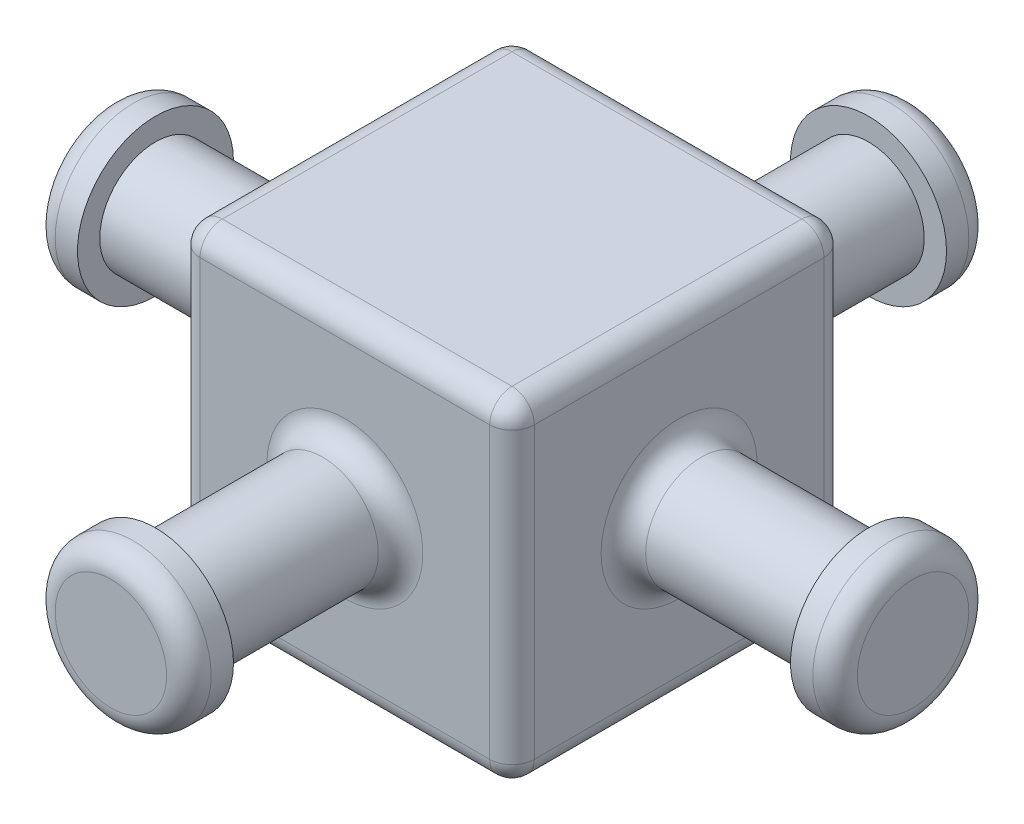
SolidWorks part; units mm, degrees
ref_plane "Front Plane" through (0, 0, 0) normal (0, 0, 1) x (1, 0, 0)
ref_plane "Top Plane" through (0, 0, 0) normal (0, 1, 0) x (1, 0, 0)
ref_plane "Right Plane" through (0, 0, 0) normal (1, 0, 0) x (0, 0, -1)
sketch "Sketch1" plane through (0, 0, 0) normal (0, 0, 1) x (1, 0, 0)
  circle A0 centre (0, 0) radius 3.175
  dimension "D1" = 6.35
extrude "Boss-Extrude1" add sketch "Sketch1" along normal mid plane 40.64
sketch "Sketch2" plane through (0, 0, 20.32) normal (0, 0, 1) x (1, 0, 0)
  circle A0 centre (0, 0) radius 4.445
  dimension "D1" = 8.89
extrude "Boss-Extrude2" add sketch "Sketch2" along normal blind 2.54
fillet "Fillet1" radius 1.27 1 edges at (4.445, 0, 22.86)
mirror "Mirror1" about plane through (0, 0, 0) normal (0, 0, 1) of "Fillet1", "Boss-Extrude2"
sketch "Sketch3" plane through (0, 0, 0) normal (1, 0, 0) x (0, 0, -1)
  line L0 (20.32, 3.175) -> (-20.32, 3.175) construction
  circle A0 centre (0, 0) radius 3.175
extrude "Boss-Extrude3" add sketch "Sketch3" along normal mid plane 40.64
sketch "Sketch4" plane through (20.32, 0, 0) normal (1, 0, 0) x (0, 0, -1)
  circle A0 centre (0, 0) radius 4.445
  dimension "D1" = 8.89
extrude "Boss-Extrude4" add sketch "Sketch4" along normal blind 2.54
fillet "Fillet2" radius 1.27 1 edges at (22.86, 0, -4.445)
mirror "Mirror2" about plane through (0, 0, 0) normal (1, 0, 0) of "Fillet2", "Boss-Extrude4"
sketch "Sketch5" plane through (0, 0, 0) normal (1, 0, 0) x (0, 0, -1)
  line L1 (-9.525, -9.525) -> (9.525, -9.525)
  line L2 (-9.525, -9.525) -> (-9.525, 9.525)
  line L3 (-9.525, 9.525) -> (9.525, 9.525)
  line L4 (9.525, -9.525) -> (9.525, 9.525)
  line L5 (-9.525, -9.525) -> (9.525, 9.525) construction
  line L6 (-9.525, 9.525) -> (9.525, -9.525) construction
  point P0 (0, 0)
  dimension "D2" = 19.05
extrude "Boss-Extrude5" add sketch "Sketch5" along normal mid plane 19.05
fillet "Fillet3" radius 1.27 16 edges at (-3.175, 0, 9.525) (0, -9.525, 9.525) (-9.525, 0, 3.175) (-9.525, 0, 9.525) (-9.525, -9.525, 0) (0, 9.525, 9.525) (-9.525, 9.525, 0) (3.175, 0, -9.525) (0, -9.525, -9.525) (0, 9.525, -9.525) (-9.525, 0, -9.525) (9.525, 0, 3.175) (9.525, -9.525, 0) (9.525, 0, 9.525) (9.525, 9.525, 0) (9.525, 0, -9.525)
